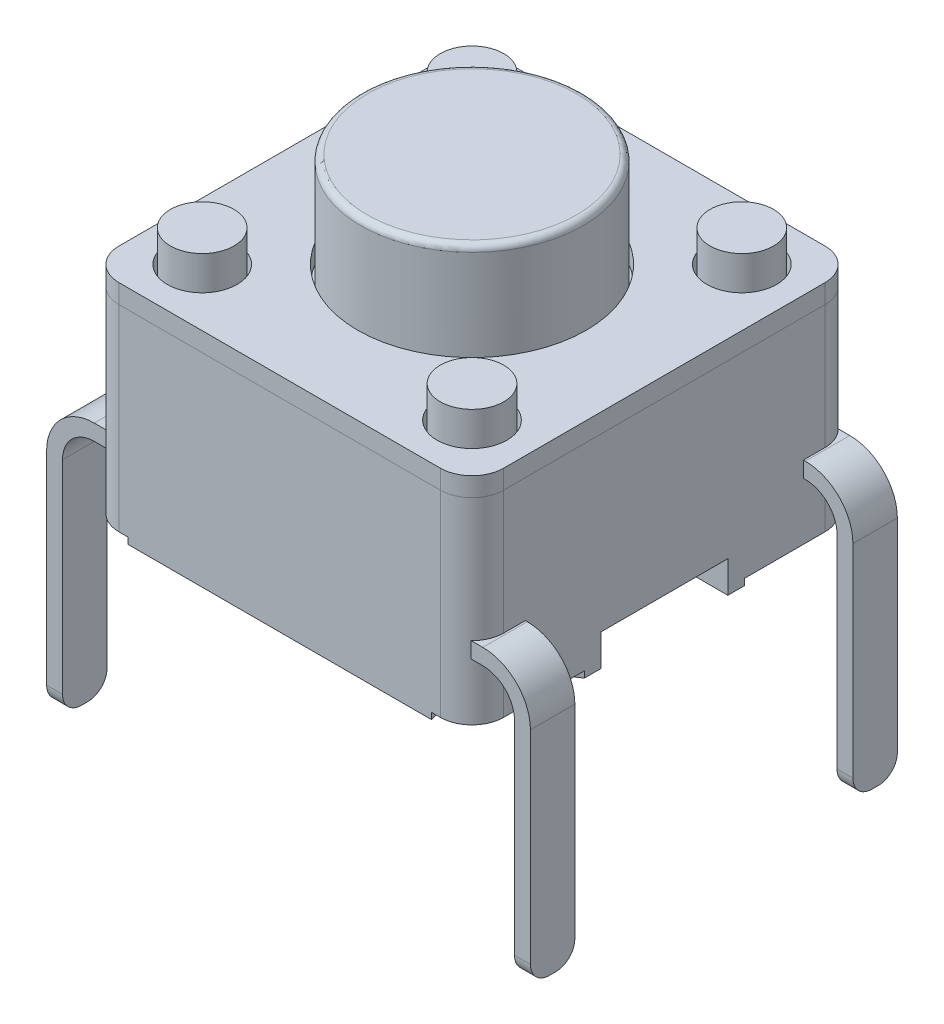
SolidWorks part; units mm, degrees
material "ABS"
ref_plane "Front Plane" through (0, 0, 0) normal (0, 0, 1) x (1, 0, 0)
ref_plane "Top Plane" through (0, 0, 0) normal (0, 1, 0) x (1, 0, 0)
ref_plane "Right Plane" through (0, 0, 0) normal (1, 0, 0) x (0, 0, -1)
sketch "Sketch1" plane through (0, 0, 0) normal (0, 1, 0) x (1, 0, 0)
  line L1 (-3.03, 3.03) -> (3.03, 3.03)
  line L2 (-3.03, 3.03) -> (-3.03, -3.03)
  line L3 (-3.03, -3.03) -> (3.03, -3.03)
  line L4 (3.03, 3.03) -> (3.03, -3.03)
  line L5 (-3.03, 3.03) -> (3.03, -3.03) construction
  line L6 (-3.03, -3.03) -> (3.03, 3.03) construction
  point P0 (0, 0)
  dimension "D1" = 6.06
  dimension "D2" = 6.06
extrude "Boss-Extrude1" add sketch "Sketch1" against normal blind 0.3
sketch "Sketch2" plane through (0, -0.3, 0) normal (0, -1, 0) x (1, 0, 0)
  line L4 (3.03, -3.03) -> (3.03, 3.03)
  line L5 (3.03, 3.03) -> (-3.03, 3.03)
  line L6 (-3.03, 3.03) -> (-3.03, -3.03)
  line L7 (-3.03, -3.03) -> (3.03, -3.03)
  line L8 (3.03, -3.03) -> (3.03, 3.03)
  line L9 (3.03, 3.03) -> (-3.03, 3.03)
  line L10 (-3.03, 3.03) -> (-3.03, -3.03)
  line L11 (-3.03, -3.03) -> (3.03, -3.03)
  dimension "D1" = 0
extrude "Boss-Extrude2" add sketch "Sketch2" along normal blind 3.2 separate body
sketch "Sketch3" plane through (0, 0, 0) normal (0, 1, 0) x (1, 0, 0)
  line L1 (-2.125, 2.125) -> (2.125, 2.125) construction
  line L2 (-2.125, 2.125) -> (-2.125, -2.125) construction
  line L3 (-2.125, -2.125) -> (2.125, -2.125) construction
  line L4 (2.125, 2.125) -> (2.125, -2.125) construction
  line L5 (-2.125, 2.125) -> (2.125, -2.125) construction
  line L6 (-2.125, -2.125) -> (2.125, 2.125) construction
  circle A0 centre (0, 0) radius 1.8
  circle A1 centre (2.125, 2.125) radius 0.55
  circle A2 centre (2.125, -2.125) radius 0.55
  circle A3 centre (-2.125, -2.125) radius 0.55
  circle A4 centre (-2.125, 2.125) radius 0.55
  dimension "D1" = 1.1
  dimension "D3" = 3.6
  dimension "D2" = 4.25
extrude "Cut-Extrude1" cut sketch "Sketch3" against normal up to surface (0.3 mm away) up to face at (0, -0.3, 0)
fillet "Fillet1" radius 0.5 4 edges at (-3.03, -0.15, -3.03) (3.03, -0.15, -3.03) (3.03, -0.15, 3.03) (-3.03, -0.15, 3.03)
fillet "Fillet2" radius 0.5 4 edges at (-3.03, -1.9, -3.03) (3.03, -1.9, -3.03) (3.03, -1.9, 3.03) (-3.03, -1.9, 3.03)
sketch "Sketch5" plane through (0, -0.3, 0) normal (0, 1, 0) x (1, 0, 0)
  circle A0 centre (-2.125, 2.125) radius 0.5
  circle A1 centre (2.125, 2.125) radius 0.5
  circle A2 centre (2.125, -2.125) radius 0.5
  circle A3 centre (-2.125, -2.125) radius 0.5
  dimension "D1" = 1
extrude "Boss-Extrude4" add sketch "Sketch5" along normal offset from surface (0.8 mm away) 4 up to face at (0, -3.5, 0)
sketch "Sketch6" plane through (0, -0.3, 0) normal (0, 1, 0) x (1, 0, 0)
  circle A0 centre (0, 0) radius 1.75
  dimension "D1" = 3.5
extrude "Boss-Extrude5" add sketch "Sketch6" along normal offset from surface (1.8 mm away) 5 separate body up to face at (0, -3.5, 0)
fillet "Fillet4" radius 0.1 1 edges at (0, 1.5, -1.75)
sketch "Sketch7" plane through (3.03, 0, 0) normal (1, 0, 0) x (0, 0, -1)
  line L0 (0, 0) -> (0, -3) construction
  line L1 (2.53, -3.5) -> (-2.53, -3.5) construction
  line L2 (-1, -3) -> (1, -3)
  line L3 (-1, -3) -> (-1, -3.5)
  line L4 (-1, -3.5) -> (1, -3.5)
  line L5 (1, -3) -> (1, -3.5)
  dimension "D1" = 3
  dimension "D2" = 2
extrude "Cut-Extrude2" cut sketch "Sketch7" against normal up to surface (6.06 mm away) up to face at (-3.03, -1.9, 0)
ref_plane "Plane1" through (0, 0, 2.54) normal (0, 0, 1) x (1, 0, 0)
sketch "Sketch8" plane through (0, 0, 2.54) normal (0, 0, 1) x (1, 0, 0)
  line L0 (0, 0) -> (0, -2.25) construction
  line L1 (-3.06, -2.25) -> (3.06, -2.25)
  line L2 (-3.81, -3) -> (-3.81, -6.5)
  line L3 (3.81, -3) -> (3.81, -6.5)
  line L4 (3.81, -6.5) -> (-3.81, -6.5) construction
  line L5 (0, -2.25) -> (0, -6.5) construction
  arc A0 (-3.06, -2.25) -> (-3.81, -3) centre (-3.06, -3) ccw
  arc A1 (3.06, -2.25) -> (3.81, -3) centre (3.06, -3) cw
  dimension "D4" = 0.75
  dimension "D1" = 7.62
  dimension "D2" = 2.25
  dimension "D3" = 6.5
extrude "Extrude-Thin1" add sketch "Sketch8" against normal mid plane 0.7 separate body thin
fillet "Fillet5" radius 0.3 4 edges at (3.685, -6.5, 2.19) (3.685, -6.5, 2.89) (-3.685, -6.5, 2.19) (-3.685, -6.5, 2.89)
pattern_linear "LPattern1" count 2 spacing 5.08 along (0, 0, -1) of bodies 114
sketch "Sketch9" plane through (0, -3.5, 0) normal (0, -1, 0) x (1, 0, 0)
  line L1 (-3.81, 2.54) -> (3.81, 2.54) construction
  line L2 (-3.81, 2.54) -> (-3.81, -2.54) construction
  line L3 (-3.81, -2.54) -> (3.81, -2.54) construction
  line L4 (3.81, 2.54) -> (3.81, -2.54) construction
  line L5 (-3.81, 2.54) -> (3.81, -2.54) construction
  line L6 (-3.81, -2.54) -> (3.81, 2.54) construction
  circle A0 centre (-3.81, 2.54) radius 1.5
  circle A1 centre (3.81, 2.54) radius 1.5
  circle A2 centre (3.81, -2.54) radius 1.5
  circle A3 centre (-3.81, -2.54) radius 1.5
  point P0 (0, 0)
  dimension "D3" = 3
  dimension "D1" = 7.62
  dimension "D2" = 5.08
extrude "Cut-Extrude4" cut sketch "Sketch9" against normal blind 0.1
